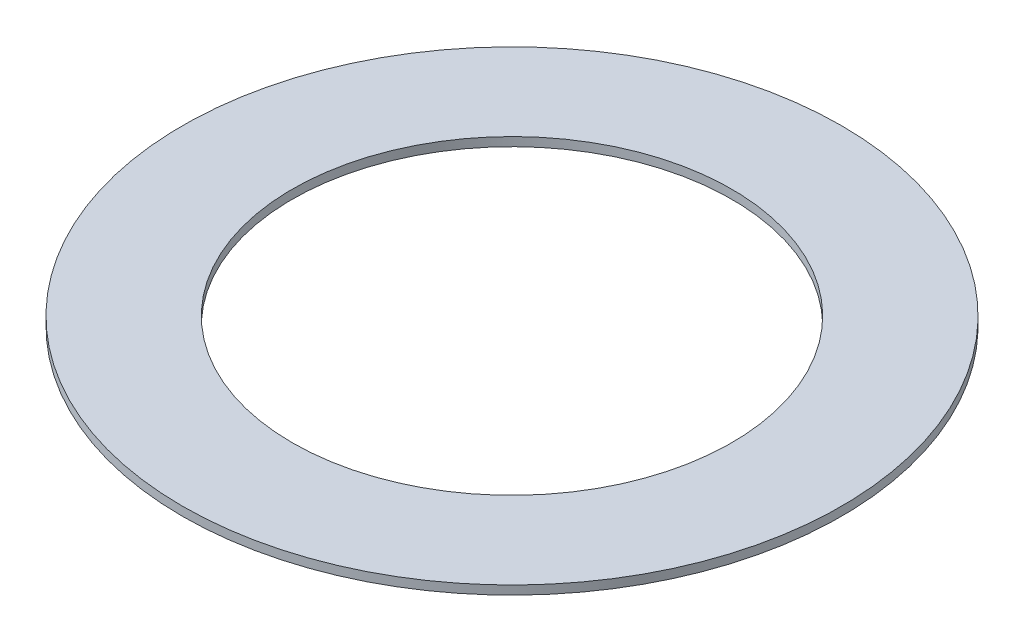
SolidWorks part; units mm, degrees
material "Plain Carbon Steel"
ref_plane "Front-Back Midplane" through (0, 0, 0) normal (0, 0, 1) x (1, 0, 0)
ref_plane "Horizontal Midplane" through (0, 0, 0) normal (0, 1, 0) x (1, 0, 0)
ref_plane "Left-Right Midplane" through (0, 0, 0) normal (1, 0, 0) x (0, 0, -1)
ref_axis "Axis1" through (0, 52.5, 0) along (0, -1, 0)
sketch "Sketch1" plane through (0, 0, 0) normal (0, 0, 1) x (1, 0, 0)
  line L1 (-3.175, 0) -> (-4.7625, 0)
  line L2 (-3.175, 0) -> (-3.175, 0.127)
  line L3 (-3.175, 0.127) -> (-4.7625, 0.127)
  line L4 (-4.7625, 0) -> (-4.7625, 0.127)
  dimension "D1" = 3.175
  dimension "D2" = 4.7625
  dimension "D3" = 0.127
revolve "Revolve1" add sketch "Sketch1" angle 360 about axis through (0, 52.5, 0) along (0, -1, 0)
